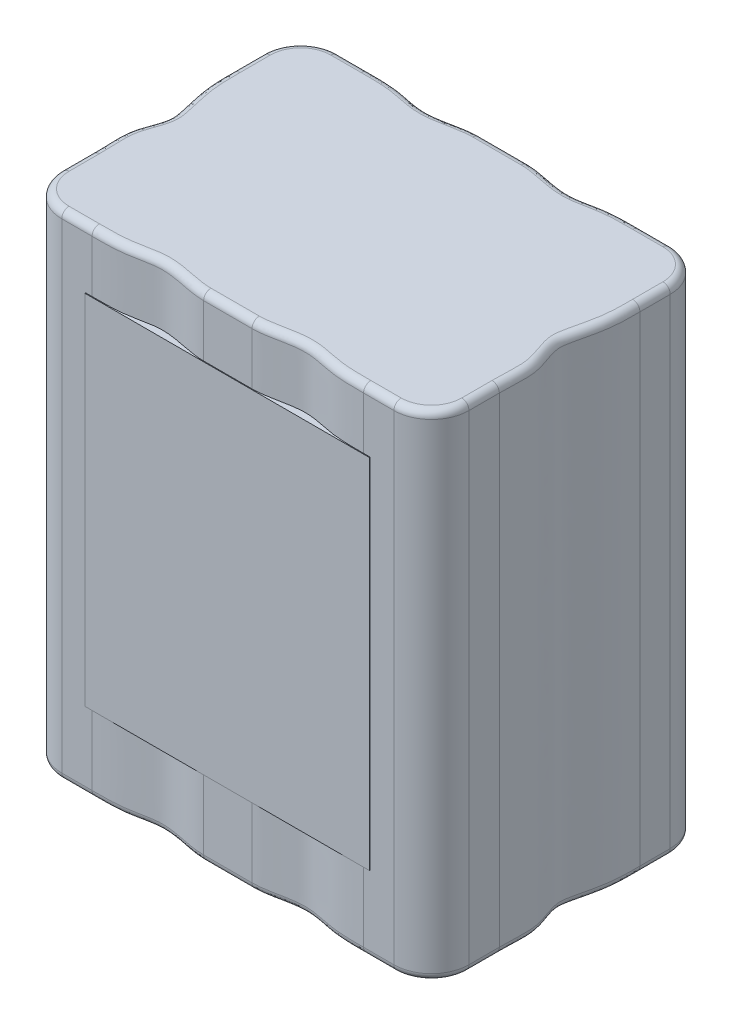
SolidWorks part; units mm, degrees
ref_plane "前视基准面" through (0, 0, 0) normal (0, 0, 1) x (1, 0, 0)
ref_plane "上视基准面" through (0, 0, 0) normal (0, 1, 0) x (1, 0, 0)
ref_plane "右视基准面" through (0, 0, 0) normal (1, 0, 0) x (0, 0, -1)
sketch "草图1" plane through (0, 0, 0) normal (0, 1, 0) x (1, 0, 0)
  line L0 (18.6667, -9.6667) -> (-18.6667, -9.6667) construction
  line L1 (-28, 19) -> (28, 19) construction
  line L2 (-28, 19) -> (-28, -19) construction
  line L3 (-28, -19) -> (28, -19) construction
  line L4 (28, 19) -> (28, -19) construction
  line L5 (-28, 19) -> (28, -19) construction
  line L6 (-28, -19) -> (28, 19) construction
  line L7 (18.6667, 9.6667) -> (-18.6667, 9.6667) construction
  line L8 (0, 9.6667) -> (0, -9.6667) construction
  line L9 (0, 0) -> (12.754, 0) construction
  line L10 (-22.8357, 19) -> (-18.6667, 19)
  line L11 (-28, 13.8357) -> (-28, 9.6667)
  line L12 (3.3276, 19) -> (-3.3276, 19)
  line L13 (-28, -13.8357) -> (-28, -9.6667)
  line L14 (-22.8357, -19) -> (-18.6667, -19)
  line L15 (3.3276, -19) -> (-3.3276, -19)
  line L16 (22.8357, -19) -> (18.6667, -19)
  line L17 (28, -13.8357) -> (28, -9.6667)
  line L18 (28, 13.8357) -> (28, 9.6667)
  line L19 (22.8357, 19) -> (18.6667, 19)
  circle A0 centre (18.6667, -9.6667) radius 9.3333 construction
  circle A1 centre (0, -9.6667) radius 9.3333 construction
  circle A2 centre (-18.6667, -9.6667) radius 9.3333 construction
  circle A3 centre (18.6667, 9.6667) radius 9.3333 construction
  circle A4 centre (0, 9.6667) radius 9.3333 construction
  circle A5 centre (-18.6667, 9.6667) radius 9.3333 construction
  arc A6 (-22.8357, 19) -> (-28, 13.8357) centre (-22.8357, 13.8357) ccw
  arc A7 (-22.8357, -19) -> (-28, -13.8357) centre (-22.8357, -13.8357) cw
  arc A8 (22.8357, -19) -> (28, -13.8357) centre (22.8357, -13.8357) ccw
  arc A9 (22.8357, 19) -> (28, 13.8357) centre (22.8357, 13.8357) cw
  spline S0 degree 3 poles (-18.6667, 19) (-17.0533, 19) (-14.2278, 19.0144) (-10.1186, 17.8305) (-6.5523, 18.5913) (-4.3146, 19) (-3.3276, 19) knots 0 0 0 0 0.301969 0.562471 0.806411 1 1 1 1
  spline S1 degree 3 poles (-18.6667, -19) (-17.0533, -19) (-14.2278, -19.0144) (-10.1186, -17.8305) (-6.5523, -18.5913) (-4.3146, -19) (-3.3276, -19) knots 0 0 0 0 0.301969 0.562471 0.806411 1 1 1 1
  spline S2 degree 3 poles (-28, 9.6667) (-28, 8.5133) (-28.0662, 5.2978) (-26.7452, 0.9829) (-26.7476, -1.0953) (-28.4277, -4.82) (-28, -6.7672) (-28, -9.6667) knots 0 0 0 0 0.169964 0.367132 0.412787 0.626512 1 1 1 1
  spline S3 degree 3 poles (18.6667, -19) (17.0533, -19) (14.2278, -19.0144) (10.1186, -17.8305) (6.5523, -18.5913) (4.3146, -19) (3.3276, -19) knots 0 0 0 0 0.301969 0.562471 0.806411 1 1 1 1
  spline S4 degree 3 poles (28, 9.6667) (28, 8.5133) (28.0662, 5.2978) (26.7452, 0.9829) (26.7476, -1.0953) (28.4277, -4.82) (28, -6.7672) (28, -9.6667) knots 0 0 0 0 0.169964 0.367132 0.412787 0.626512 1 1 1 1
  spline S5 degree 3 poles (18.6667, 19) (17.0533, 19) (14.2278, 19.0144) (10.1186, 17.8305) (6.5523, 18.5913) (4.3146, 19) (3.3276, 19) knots 0 0 0 0 0.301969 0.562471 0.806411 1 1 1 1
  point P0 (0, 0)
  point P24 (0, 0)
  point P41 (-26.7526, 0)
  point P43 (0, 0)
  point P46 (0, -19)
  point P66 (0, 19)
  point P67 (-22.8357, 13.8357)
  dimension "D1" = 38
  dimension "D2" = 56
extrude "凸台-拉伸1" add sketch "草图1" along normal blind 68
fillet "圆角1" radius 1 40 edges at (-28, 0, -11.7512) (-28, 0, 11.7512) (-26.4874, 0, 17.4874) (-20.7512, 0, 19) (0, 0, 19) (20.7512, 0, 19) (26.4874, 0, 17.4874) (28, 0, 11.7512) (28, 0, -11.7512) (26.4874, 0, -17.4874) (20.7512, 0, -19) (0, 0, -19) (-20.7512, 0, -19) (-26.4874, 0, -17.4874) (-20.7512, 68, -19) (0, 68, -19) (20.7512, 68, -19) (26.4874, 68, -17.4874) (28, 68, -11.7512) (28, 68, 11.7512) (26.4874, 68, 17.4874) (20.7512, 68, 19) (0, 68, 19) (-20.7512, 68, 19) (-26.4874, 68, 17.4874) (-28, 68, 11.7512) (-28, 68, -11.7512) (-26.4874, 68, -17.4874)
sketch "草图2" plane through (0, 0, 19) normal (0, 0, 1) x (1, 0, 0)
  line L1 (-19.5556, 59.8208) -> (19.5556, 59.8208)
  line L2 (-19.5556, 59.8208) -> (-19.5556, 10.6296)
  line L3 (-19.5556, 10.6296) -> (19.5556, 10.6296)
  line L4 (19.5556, 59.8208) -> (19.5556, 10.6296)
  line L5 (-19.5556, 59.8208) -> (19.5556, 10.6296) construction
  line L6 (-19.5556, 10.6296) -> (19.5556, 59.8208) construction
  point P0 (0, 35.2252)
extrude "凸台-拉伸2" add sketch "草图2" along normal blind 0.1 and the other way blind 15
